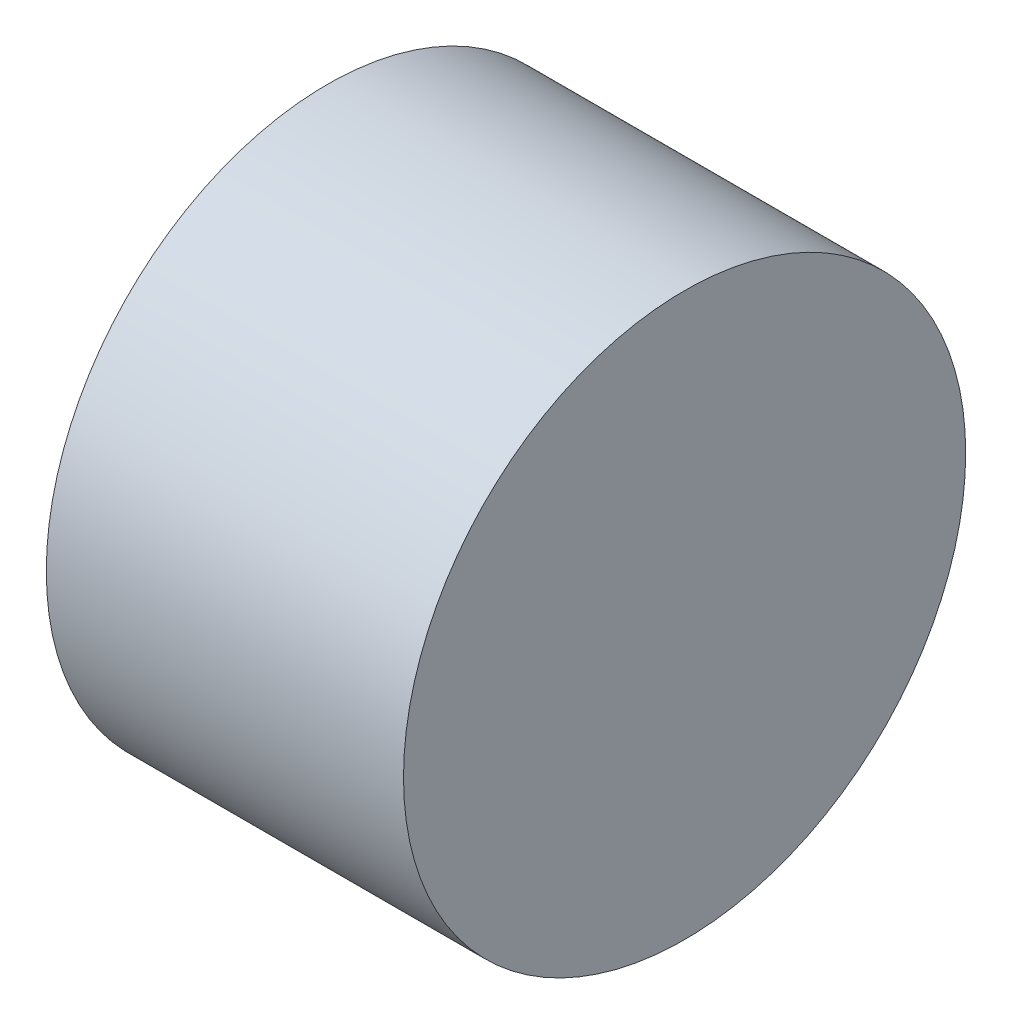
SolidWorks part; units mm, degrees
ref_plane "Front Plane" through (0, 0, 0) normal (0, 0, 1) x (1, 0, 0)
ref_plane "Top Plane" through (0, 0, 0) normal (0, 1, 0) x (1, 0, 0)
ref_plane "Right Plane" through (0, 0, 0) normal (1, 0, 0) x (0, 0, -1)
sketch "Sketch1" plane through (0, 0, 0) normal (0, 0, 1) x (1, 0, 0)
  line L0 (8.255, 0) -> (-8.255, 0) construction
  line L1 (31.255, 0) -> (-31.255, 0) construction
  line L2 (8.255, 0) -> (8.255, 18.1)
  line L3 (8.255, 18.1) -> (31.255, 18.1)
  line L4 (31.255, 18.1) -> (31.255, 0)
  line L5 (8.255, 0) -> (31.255, 0)
  point P4 (0, 0)
  point P8 (0, 0)
  dimension "D1" = 23
  dimension "D2" = 16.51
  dimension "D3" = 18.1
revolve "Revolve1" add sketch "Sketch1" angle 360 about L5
sketch "Sketch2" plane through (8.255, 0, 0) normal (-1, 0, 0) x (0, 0, 1)
  circle A0 centre (0, 0) radius 3.7147
  dimension "D1" = 7.4295
extrude "Cut-Extrude1" cut sketch "Sketch2" against normal blind 8.5725
sketch "Sketch3" plane through (31.255, 0, 0) normal (1, 0, 0) x (0, 0, -1)
  line L0 (-20.8953, -55) -> (-20.8953, -46.1532)
  line L1 (13.175, -55) -> (-13.175, -55) construction
  line L2 (13.175, -55) -> (13.175, 55) construction
  line L3 (13.175, 55) -> (-13.175, 55) construction
  line L4 (-13.175, -55) -> (-13.175, 55) construction
  line L5 (13.175, -55) -> (-13.175, 55) construction
  line L6 (13.175, 55) -> (-13.175, -55) construction
  line L7 (-24.3823, -32.1152) -> (-32.3245, -17.1152)
  line L9 (-5.4548, -55) -> (-5.4548, -44)
  line L11 (5.4547, -44) -> (5.4547, -55)
  line L12 (20.8953, -55) -> (20.8953, -46.1532)
  line L13 (24.3823, -32.1152) -> (32.3245, -17.1152)
  line L14 (55, 0) -> (-55, 0) construction
  line L15 (13.175, -55) -> (-13.175, 55) construction
  line L16 (13.175, 55) -> (-13.175, -55) construction
  line L17 (13.175, 55) -> (-13.175, 55) construction
  line L18 (24.3823, 32.1152) -> (32.3245, 17.1152)
  line L19 (20.8953, 55) -> (20.8953, 46.1532)
  line L20 (5.4547, 44) -> (5.4547, 55)
  line L21 (-5.4548, 55) -> (-5.4548, 44)
  line L22 (-24.3823, 32.1152) -> (-32.3245, 17.1152)
  line L23 (-20.8953, 55) -> (-20.8953, 46.1532)
  arc A15 (32.3245, -17.1152) -> (32.3245, 17.1152) centre (0, 0) ccw
  arc A16 (-5.4548, 55) -> (-20.8953, 55) centre (-13.175, 55) ccw
  arc A17 (-20.8953, -55) -> (-5.4548, -55) centre (-13.175, -55) ccw
  arc A18 (5.4547, -55) -> (20.8953, -55) centre (13.175, -55) ccw
  arc A19 (20.8953, 55) -> (5.4547, 55) centre (13.175, 55) ccw
  arc A20 (-5.4548, -44) -> (5.4547, -44) centre (0, -44) cw
  arc A21 (20.8953, -46.1532) -> (24.3823, -32.1152) centre (50.8953, -46.1532) cw
  arc A22 (-20.8953, -46.1532) -> (-24.3823, -32.1152) centre (-50.8953, -46.1532) ccw
  arc A23 (-20.8953, 46.1532) -> (-24.3823, 32.1152) centre (-50.8953, 46.1532) cw
  arc A24 (20.8953, 46.1532) -> (24.3823, 32.1152) centre (50.8953, 46.1532) ccw
  arc A25 (-5.4548, 44) -> (5.4547, 44) centre (0, 44) ccw
  arc A26 (5.4547, 55) -> (20.8953, 55) centre (13.175, 55) cw
  arc A27 (-20.8953, 55) -> (-5.4548, 55) centre (-13.175, 55) cw
  arc A29 (-32.3245, 17.1152) -> (-32.3245, -17.1152) centre (0, 0) ccw
  dimension "D3" = 15.4405
  dimension "D5" = 7.7203
  dimension "D4" = 30
  dimension "D7" = 15
  dimension "D9" = 110
  dimension "D1" = 73.152
  dimension "D6" = 15
  dimension "D2" = 26.35
  dimension "D8" = 11
